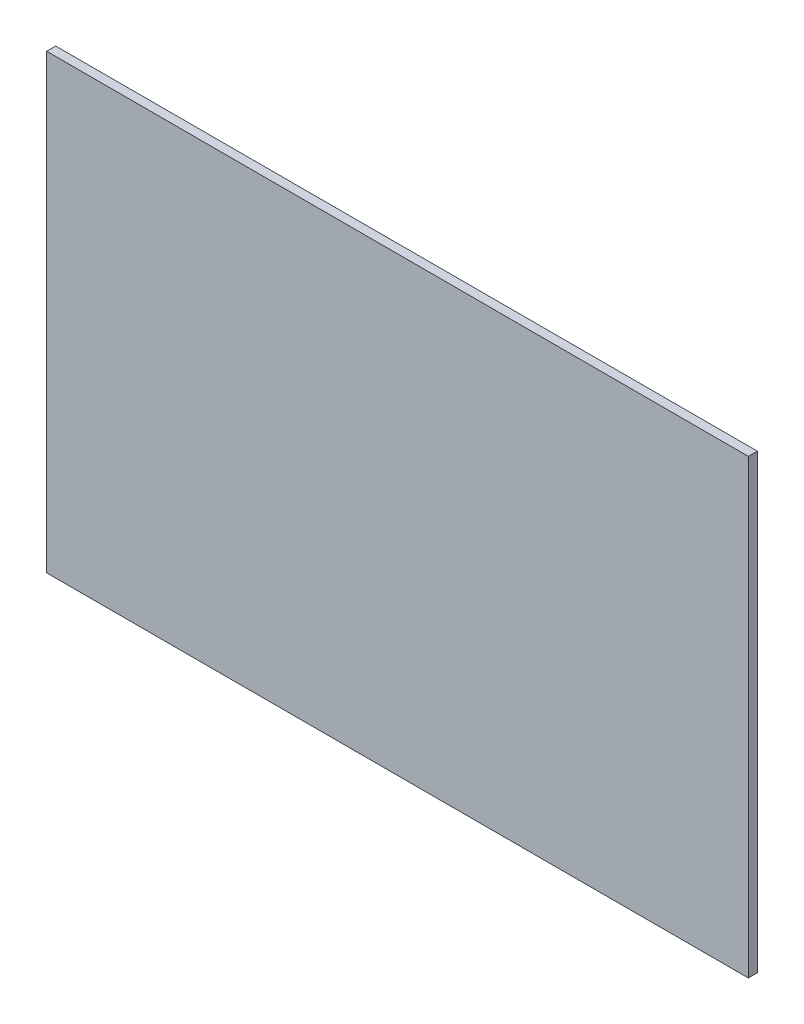
SolidWorks part; units mm, degrees
ref_plane "Front Plane" through (0, 0, 0) normal (0, 0, 1) x (1, 0, 0)
ref_plane "Top Plane" through (0, 0, 0) normal (0, 1, 0) x (1, 0, 0)
ref_plane "Right Plane" through (0, 0, 0) normal (1, 0, 0) x (0, 0, -1)
sketch "Sketch1" plane through (0, 0, 0) normal (0, 0, 1) x (1, 0, 0)
  line L1 (72.9141, -76.938) -> (116.5, -76.938) construction
  line L4 (58.0433, 30.3517) -> (114.1466, -76.938) construction
  line L7 (55.3848, 28.9615) -> (110.7612, -76.938) construction
  line L8 (-58.0433, -30.3517) -> (14.8708, -169.7896) construction
  line L9 (-55.3848, -28.9615) -> (17.5292, -168.3995) construction
  line L42 (42.5, 40) -> (77.5, 40) construction
  line L43 (42.5, 40) -> (42.5, -41) construction
  line L46 (116.5, -73.938) -> (72.9141, -73.938) construction
  line L47 (116.5, -204.938) -> (72.9141, -204.938) construction
  line L48 (42.5, -41) -> (77.5, -41) construction
  line L49 (77.5, 40) -> (77.5, -41) construction
  line L50 (39.5, 84) -> (103.5, 84) construction
  line L51 (49.5, 121.8401) -> (49.5, 40) construction
  line L52 (87.5, 121.8401) -> (87.5, 40) construction
  line L55 (0, 100) -> (0, -46) construction
  line L56 (-9.5, 17) -> (-9.5, -4.7961) construction
  line L57 (-39.5, -17) -> (9.7212, -17) construction
  line L58 (-39.5, 17) -> (-5.59, 17) construction
  line L63 (103.5, 84) -> (103.5, -41) construction
  line L64 (39.5, 84) -> (39.5, -41) construction
  line L65 (39.5, 17) -> (5.59, 17) construction
  line L66 (39.5, -17) -> (-9.7212, -17) construction
  line L67 (9.5, 17) -> (9.5, -4.7961) construction
  line L68 (-39.5, 84) -> (-39.5, -41) construction
  line L69 (-103.5, 84) -> (-103.5, -41) construction
  line L70 (-87.5, 121.8401) -> (-87.5, 40) construction
  line L71 (-49.5, 121.8401) -> (-49.5, 40) construction
  line L72 (-39.5, 84) -> (-103.5, 84) construction
  line L73 (-77.5, 40) -> (-77.5, -41) construction
  line L74 (-42.5, -41) -> (-77.5, -41) construction
  line L75 (-42.5, 40) -> (-42.5, -41) construction
  line L76 (-42.5, 40) -> (-77.5, 40) construction
  line L77 (-20.5, 80) -> (20.5, 80) construction
  line L78 (-116.5, 104) -> (116.5, 104)
  line L79 (-116.5, 104) -> (-116.5, -46)
  line L80 (-116.5, -46) -> (116.5, -46)
  line L81 (116.5, 104) -> (116.5, -46)
  line L82 (72.9141, -201.938) -> (116.5, -201.938) construction
  line L83 (-65.5, -62.5) -> (65.5, -62.5) construction
  line L84 (-65.5, 0) -> (-65.5, -46) construction
  line L85 (65.5, 0) -> (65.5, -46) construction
  line L86 (-60, 40) -> (-60, -41) construction
  line L87 (60, 40) -> (60, -41) construction
  line L91 (116.5, -81.4386) -> (136.4983, -119.6826) construction
  line L92 (128.2989, -110.4765) -> (132.6262, -118.7518) construction
  circle A3 centre (0, 0) radius 62.5 construction
  circle A4 centre (49.5, 84) radius 2 construction
  circle A8 centre (87.5, 84) radius 2 construction
  circle A9 centre (49.5, 53) radius 2 construction
  circle A10 centre (87.5, 53) radius 2 construction
  circle A15 centre (103.5, 24) radius 3 construction
  circle A16 centre (103.5, -27) radius 3 construction
  circle A17 centre (39.5, 17) radius 2 construction
  circle A18 centre (39.5, -17) radius 2 construction
  circle A19 centre (9.5, 17) radius 2 construction
  circle A20 centre (9.5, -17) radius 2 construction
  circle A21 centre (20.5, 80) radius 2 construction
  circle A22 centre (-20.5, 80) radius 2 construction
  circle A23 centre (-9.5, -17) radius 2 construction
  circle A24 centre (-9.5, 17) radius 2 construction
  circle A25 centre (-39.5, -17) radius 2 construction
  circle A26 centre (-39.5, 17) radius 2 construction
  circle A27 centre (-103.5, -27) radius 3 construction
  circle A28 centre (-103.5, 24) radius 3 construction
  circle A29 centre (-87.5, 53) radius 2 construction
  circle A30 centre (-49.5, 53) radius 2 construction
  circle A31 centre (-87.5, 84) radius 2 construction
  circle A32 centre (-49.5, 84) radius 2 construction
  circle A33 centre (0, 80) radius 13 construction
  circle A34 centre (0, 100) radius 2 construction
  circle A35 centre (0, 0) radius 3 construction
  arc A37 (72.9141, -76.938) -> (72.9141, -201.938) centre (72.9141, -139.438) ccw construction
  circle A38 centre (0, 0) radius 65.5 construction
  arc A39 (72.9141, -204.938) -> (72.9141, -73.938) centre (72.9141, -139.438) cw construction
  circle A40 centre (72.9141, -139.438) radius 62.5 construction
  dimension "D8" = 35
  dimension "D23" = 4
  dimension "D11" = 4
  dimension "D12" = 4
  dimension "D13" = 4
  dimension "D14" = 4
  dimension "D10" = 6
  dimension "D19" = 6
  dimension "D25" = 4
  dimension "D29" = 4
  dimension "D30" = 4
  dimension "D32" = 4
  dimension "D38" = 26
  dimension "D39" = 4
  dimension "D42" = 6
  dimension "D45" = 3
  dimension "D6" = 62.5
  dimension "D7" = 125
  dimension "D24" = 3
  dimension "D4" = 13
  dimension "D5" = 125
  dimension "D9" = 81
  dimension "D15" = 31
  dimension "D16" = 13
  dimension "D17" = 7
  dimension "D18" = 38
  dimension "D20" = 26
  dimension "D21" = 16
  dimension "D22" = 51
  dimension "D26" = 3
  dimension "D27" = 23
  dimension "D28" = 34
  dimension "D31" = 30
  dimension "D33" = 22
  dimension "D34" = 40
  dimension "D35" = 42.5
  dimension "D36" = 13
  dimension "D37" = 13
  dimension "D40" = 20
  dimension "D41" = 17
  dimension "D43" = 4
  dimension "D44" = 150
  dimension "D46" = 3
  dimension "D47" = 3
  dimension "D48" = 3
extrude "Boss-Extrude1" add sketch "Sketch1" along normal blind 3 contours A37 L1 L80 L81 L78 L79 L82 A35 A34 A33 A31 A29 A27 A25 A23 L42 L49 L48 L43 L76 L75 L74 L73 A4 A8 A9 A10 A15 A16 A17 A18
